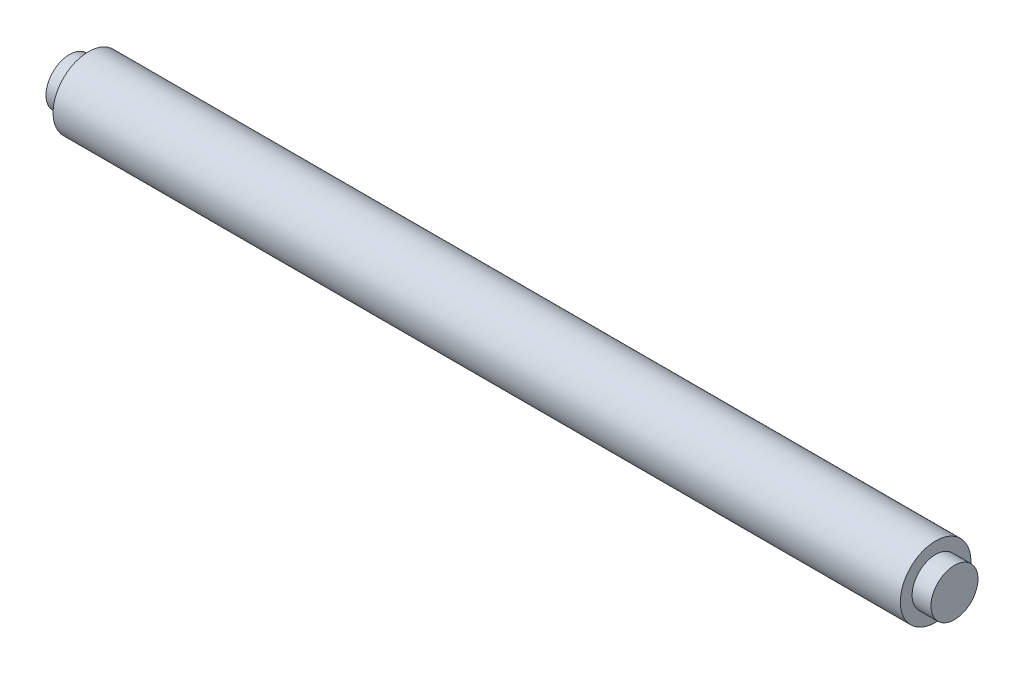
SolidWorks part; units mm, degrees
ref_plane "Front Plane" through (0, 0, 0) normal (0, 0, 1) x (1, 0, 0)
ref_plane "Top Plane" through (0, 0, 0) normal (0, 1, 0) x (1, 0, 0)
ref_plane "Right Plane" through (0, 0, 0) normal (1, 0, 0) x (0, 0, -1)
sketch "Sketch1" plane through (0, 0, 0) normal (1, 0, 0) x (0, 0, -1)
  circle A0 centre (0, 0) radius 0.75
  dimension "D1" = 1.5
extrude "Boss-Extrude1" add sketch "Sketch1" along normal blind 18
sketch "Sketch2" plane through (18, 0, 0) normal (1, 0, 0) x (0, 0, -1)
  circle A0 centre (0, 0) radius 0.5
  dimension "D1" = 1
extrude "Boss-Extrude2" add sketch "Sketch2" along normal blind 0.4
sketch "Sketch3" plane through (0, 0, 0) normal (-1, 0, 0) x (0, 0, 1)
  circle A0 centre (0, 0) radius 0.5
  dimension "D1" = 1
extrude "Boss-Extrude3" add sketch "Sketch3" along normal blind 0.4
